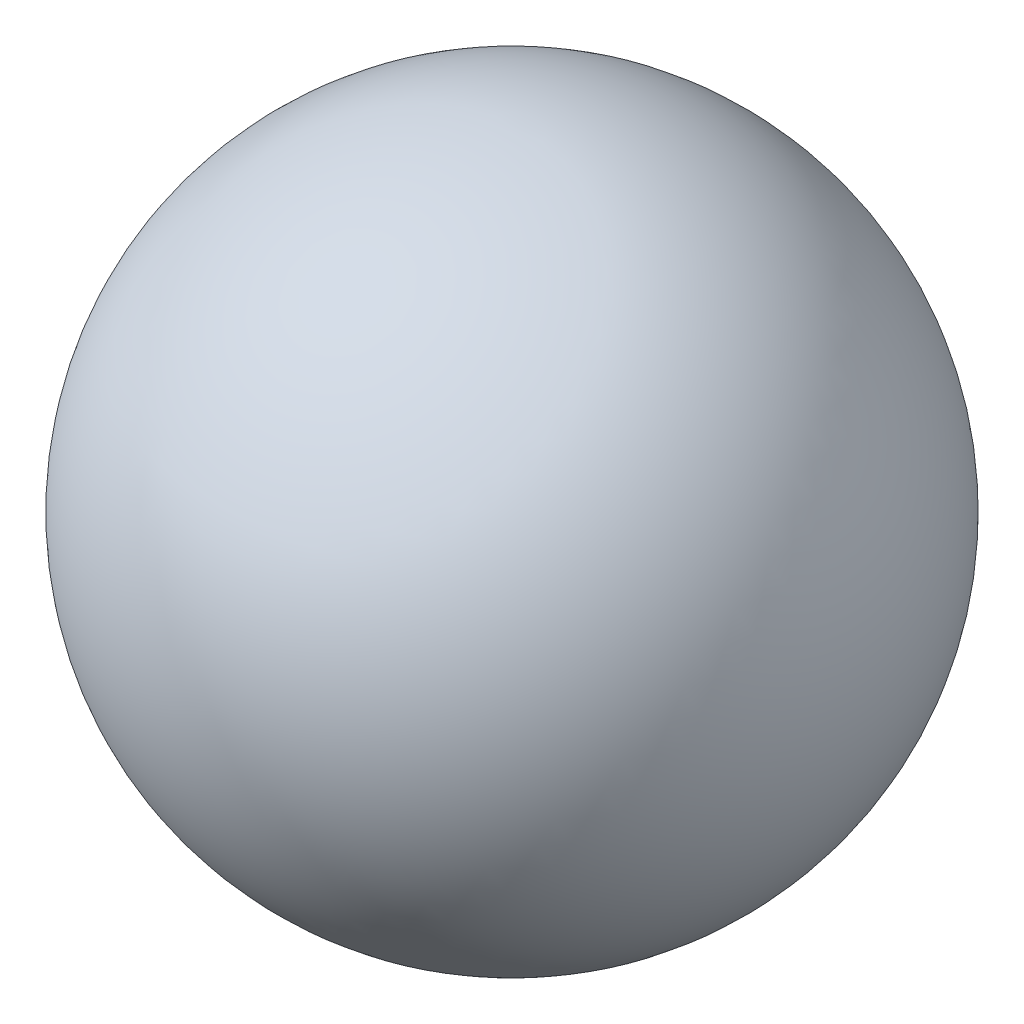
SolidWorks part; units mm, degrees
ref_plane "Front Plane" through (0, 0, 0) normal (0, 0, 1) x (1, 0, 0)
ref_plane "Top Plane" through (0, 0, 0) normal (0, 1, 0) x (1, 0, 0)
ref_plane "Right Plane" through (0, 0, 0) normal (1, 0, 0) x (0, 0, -1)
sketch "Sketch1" plane through (0, 0, 0) normal (0, 0, 1) x (1, 0, 0)
  line L0 (0, 0) -> (0, 50000) construction
  circle A0 centre (0, 0) radius 20
  dimension "D1" = 40
revolve "Revolve1" add sketch "Sketch1" angle 360 about L0
